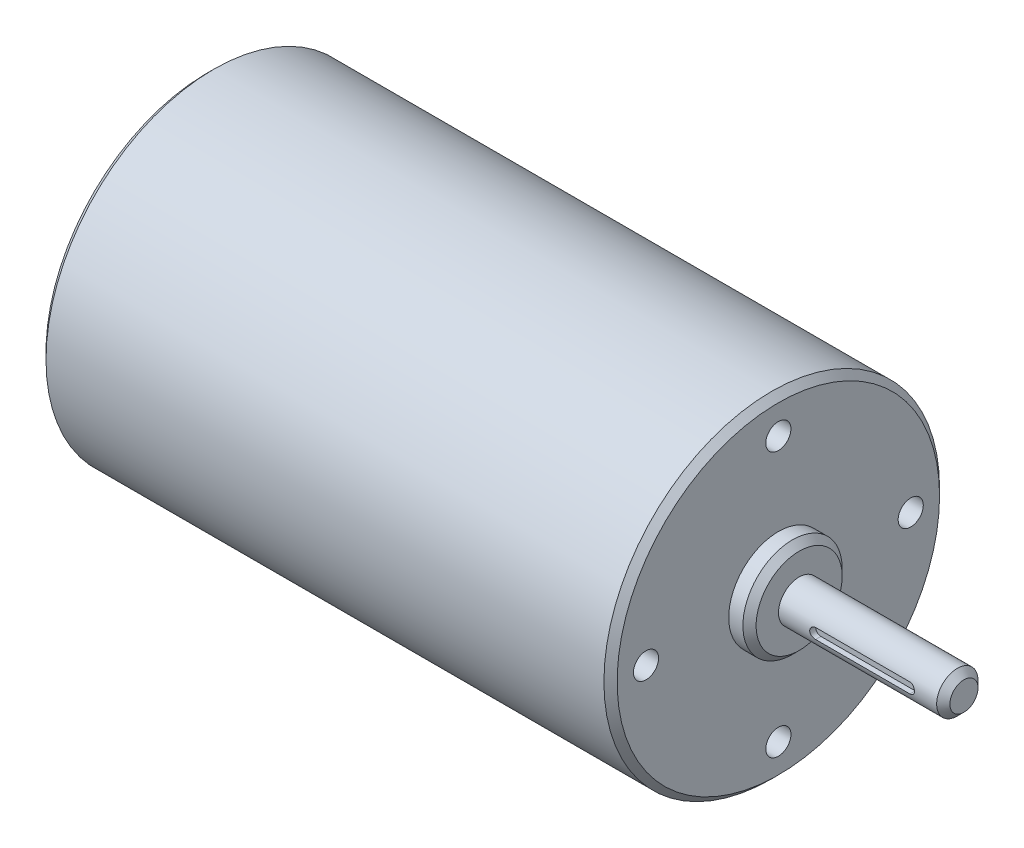
SolidWorks part; units mm, degrees
ref_plane "Front Plane" through (0, 0, 0) normal (0, 0, 1) x (1, 0, 0)
ref_plane "Top Plane" through (0, 0, 0) normal (0, 1, 0) x (1, 0, 0)
ref_plane "Right Plane" through (0, 0, 0) normal (1, 0, 0) x (0, 0, -1)
sketch "Sketch2" plane through (0, 0, 0) normal (1, 0, 0) x (0, 0, -1)
  circle A0 centre (0, 0) radius 32.2072
  dimension "D1" = 64.4144
extrude "Boss-Extrude1" add sketch "Sketch2" along normal blind 109.601
chamfer "Chamfer1" distance 1.27 angle 45 1 edges at (0, 0, -32.2072)
chamfer "Chamfer2" distance 1.27 angle 45 1 edges at (109.601, 0, -32.2072)
sketch "Sketch3" plane through (109.601, 0, 0) normal (1, 0, 0) x (0, 0, -1)
  circle A0 centre (0, 0) radius 9.525
  dimension "D1" = 19.05
extrude "Boss-Extrude2" add sketch "Sketch3" along normal blind 3.9878
sketch "Sketch4" plane through (113.5888, 0, 0) normal (1, 0, 0) x (0, 0, -1)
  circle A0 centre (0, 0) radius 3.9688
  dimension "D1" = 7.9375
extrude "Boss-Extrude3" add sketch "Sketch4" along normal blind 31.623
chamfer "Chamfer3" distance 1.27 angle 45 1 edges at (113.5888, 0, -9.525)
chamfer "Chamfer4" distance 1.27 angle 45 1 edges at (145.2118, 0, -3.9688)
sketch "Sketch5" plane through (0, 0, 0) normal (-1, 0, 0) x (0, 0, 1)
  circle A0 centre (0, 0) radius 15.24
  dimension "D1" = 30.48
extrude "Boss-Extrude4" add sketch "Sketch5" along normal blind 3.9878
chamfer "Chamfer5" distance 1.27 angle 45 1 edges at (-3.9878, 0, 15.24)
ref_plane "Plane1" through (0, 0, 3.9688) normal (0, 0, 1) x (1, 0, 0)
sketch "Sketch6" plane through (0, 0, 3.9688) normal (0, 0, 1) x (1, 0, 0)
  line L0 (120.5827, 0) -> (138.6827, 0) construction
  line L1 (120.5827, 0.9995) -> (138.6827, 0.9995)
  line L2 (120.5827, -0.9995) -> (138.6827, -0.9995)
  line L3 (113.5888, -8.255) -> (113.5888, 8.255) construction
  arc A0 (120.5827, 0.9995) -> (120.5827, -0.9995) centre (120.5827, 0) ccw
  arc A1 (138.6827, -0.9995) -> (138.6827, 0.9995) centre (138.6827, 0) ccw
  point P3 (129.6327, 0)
  dimension "D2" = 18.1
  dimension "D1" = 1.999
  dimension "D3" = 6.9939
extrude "Cut-Extrude1" cut sketch "Sketch6" against normal blind 1.1506
sketch "Sketch7" plane through (109.601, 0, 0) normal (1, 0, 0) x (0, 0, -1)
  circle A0 centre (0, 25.4) radius 2.413
  circle A1 centre (25.4, 0) radius 2.413
  circle A2 centre (0, -25.4) radius 2.413
  circle A3 centre (-25.4, 0) radius 2.413
  dimension "D1" = 4.826
  dimension "D2" = 25.4
  dimension "D3" = 4
extrude "Cut-Extrude2" cut sketch "Sketch7" against normal blind 6.35
